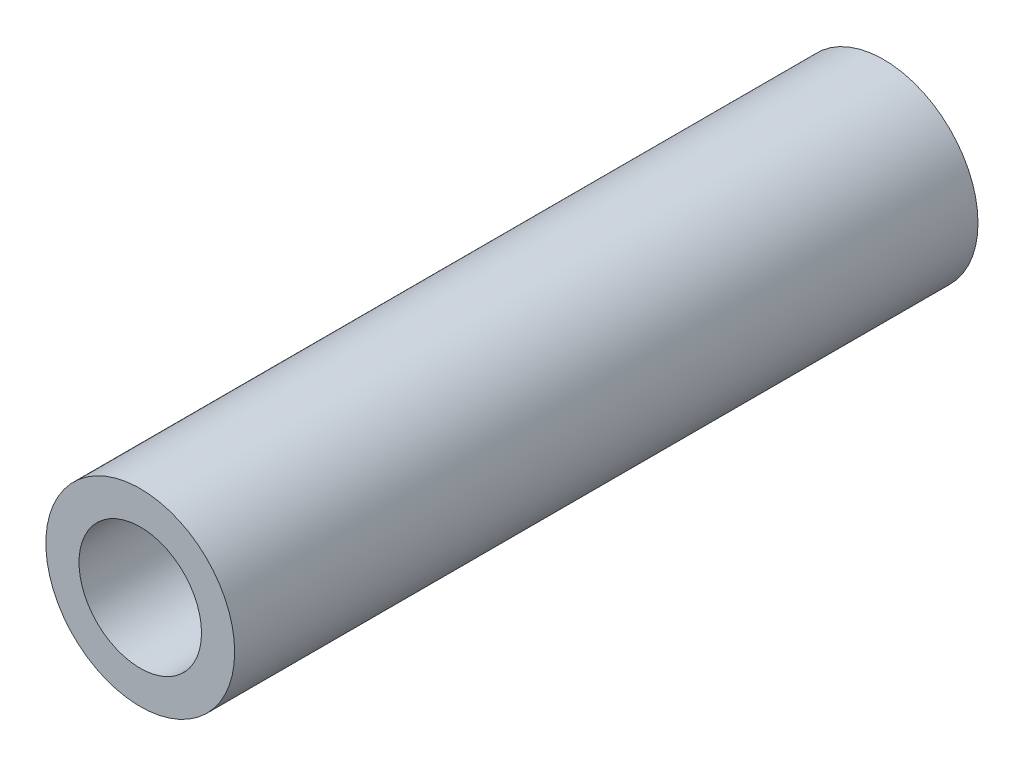
SolidWorks part; units mm, degrees
material "PVC Rigid"
ref_plane "Front Plane" through (0, 0, 0) normal (0, 0, 1) x (1, 0, 0)
ref_plane "Top Plane" through (0, 0, 0) normal (0, 1, 0) x (1, 0, 0)
ref_plane "Right Plane" through (0, 0, 0) normal (1, 0, 0) x (0, 0, -1)
sketch "Sketch1" plane through (0, 0, 0) normal (0, 0, 1) x (1, 0, 0)
  circle A0 centre (0, 0) radius 31.75
  circle A1 centre (0, 0) radius 20.6
  dimension "D1" = 63.5
  dimension "D2" = 41.2
extrude "Boss-Extrude1" add sketch "Sketch1" along normal blind 250
